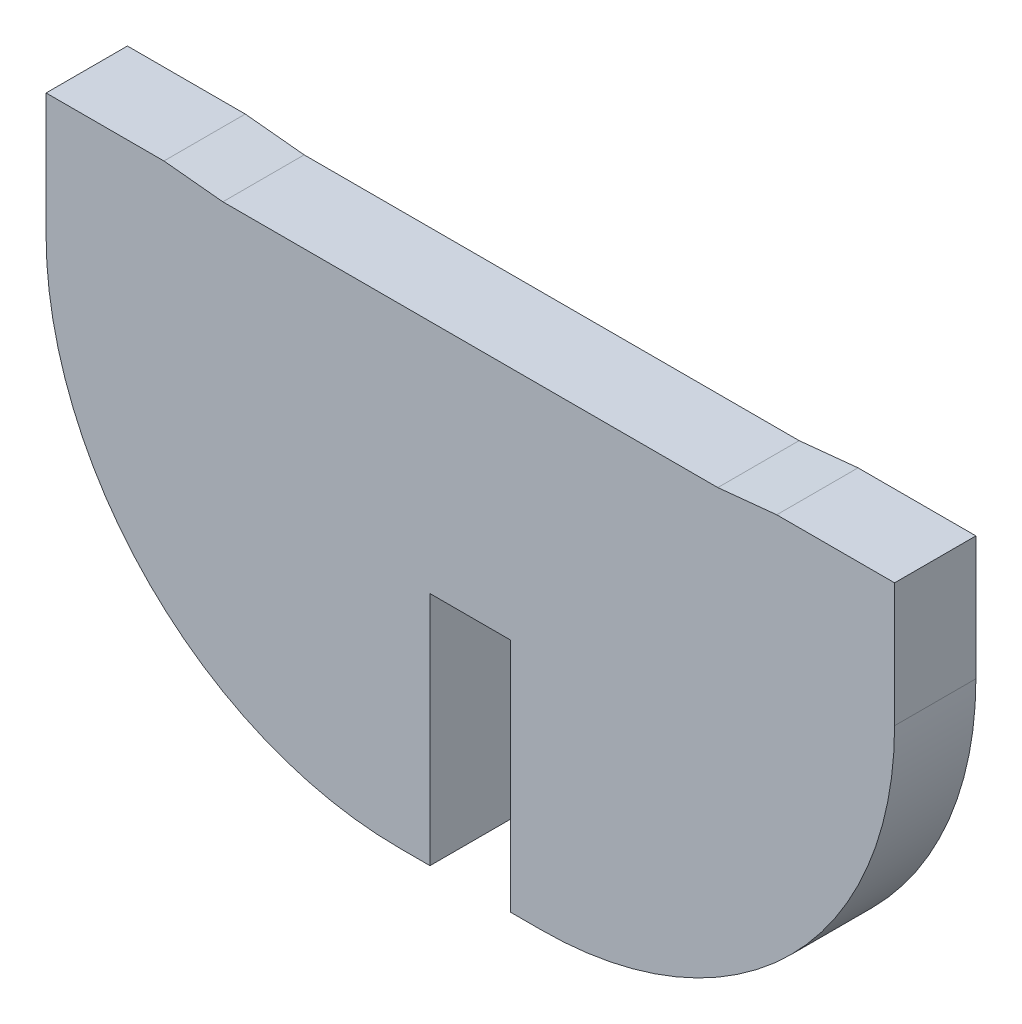
SolidWorks part; units mm, degrees
ref_plane "Front Plane" through (0, 0, 0) normal (0, 0, 1) x (1, 0, 0)
ref_plane "Top Plane" through (0, 0, 0) normal (0, 1, 0) x (1, 0, 0)
ref_plane "Right Plane" through (0, 0, 0) normal (1, 0, 0) x (0, 0, -1)
sketch "Sketch1" plane through (0, 0, 0) normal (0, 0, 1) x (1, 0, 0)
  line L1 (36, 20) -> (-36, 20)
  line L2 (36, 20) -> (36, -20)
  line L3 (36, -20) -> (-36, -20)
  line L4 (-36, 20) -> (-36, -20)
  line L5 (36, 20) -> (-36, -20) construction
  line L6 (36, -20) -> (-36, 20) construction
  point P0 (0, 0)
  dimension "D1" = 72
  dimension "D2" = 40
extrude "Boss-Extrude1" add sketch "Sketch1" along normal blind 6.9
sketch "Sketch2" plane through (0, 0, 6.9) normal (0, 0, 1) x (1, 0, 0)
  line L0 (-36, -20) -> (36, -20) construction
  line L1 (-3.425, -40) -> (3.425, -40)
  line L2 (-3.425, -40) -> (-3.425, 0)
  line L3 (-3.425, 0) -> (3.425, 0)
  line L4 (3.425, -40) -> (3.425, 0)
  line L5 (-3.425, -40) -> (3.425, 0) construction
  line L6 (-3.425, 0) -> (3.425, -40) construction
  line L7 (36, 20) -> (-36, 20) construction
  point P0 (0, -20)
  dimension "D1" = 20
  dimension "D2" = 6.85
extrude "Cut-Extrude1" cut sketch "Sketch2" against normal through all
fillet "Fillet1" radius 30 2 edges at (36, -20, 3.45) (-36, -20, 3.45)
sketch "Sketch3" plane through (0, 0, 6.9) normal (0, 0, 1) x (1, 0, 0)
  line L0 (-36, 20) -> (-36, 20.5)
  line L1 (-36, 20.5) -> (-26, 20.5)
  line L2 (-26, 20.5) -> (-21, 20)
  line L3 (36, 20) -> (-36, 20) construction
  line L4 (-21, 20) -> (-21.7492, 12.5082)
  line L5 (-21.7492, 12.5082) -> (-36, 20)
  line L6 (-36, 20) -> (-36, 10) construction
  dimension "D1" = 0.5
  dimension "D2" = 10
  dimension "D3" = 15
extrude "Boss-Extrude2" add sketch "Sketch3" against normal up to surface (6.9 mm away) up to face at (0, -3.2426, 0)
mirror "Mirror1" about plane through (0, 0, 0) normal (1, 0, 0) of "Boss-Extrude2"
sketch "Sketch4" plane through (0, 0, 6.9) normal (0, 0, 1) x (1, 0, 0)
  text T0 "SeeMeCNC\r\n 70770  R1" font "1CamBam_Stick_9" height 2
